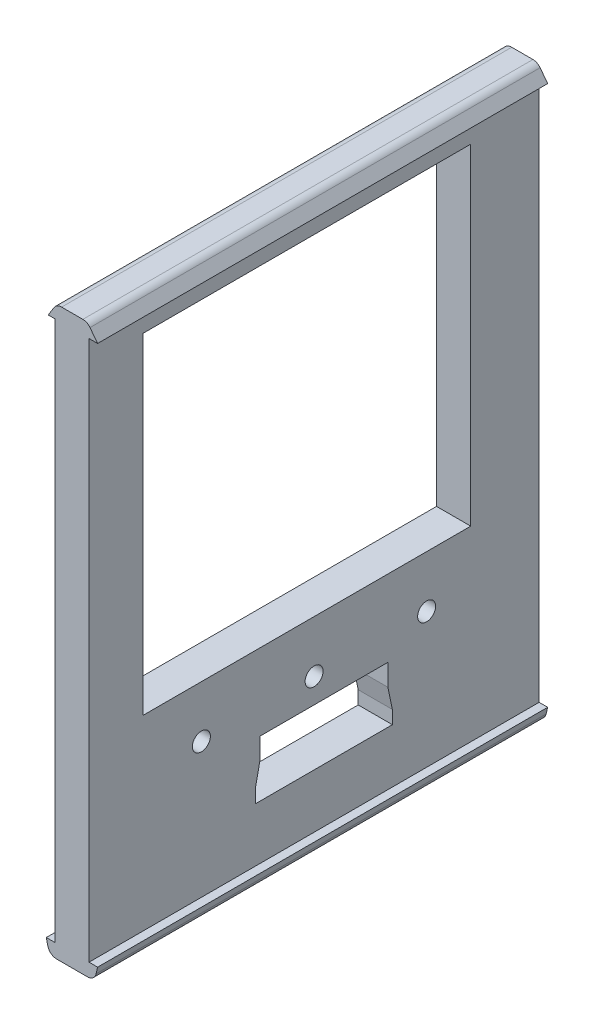
SolidWorks part; units mm, degrees
ref_plane "Plano frontal" through (0, 0, 0) normal (0, 0, 1) x (1, 0, 0)
ref_plane "Plano superior" through (0, 0, 0) normal (0, 1, 0) x (1, 0, 0)
ref_plane "Plano direito" through (0, 0, 0) normal (1, 0, 0) x (0, 0, -1)
sketch "Esboço1" plane through (0, 0, 0) normal (0, 0, 1) x (1, 0, 0)
  line L0 (0, 0) -> (0, 14.1176) construction
  line L1 (-3.8, -98.1786) -> (-5.7, -98.1786)
  line L2 (0, -101.1786) -> (0, -98.1786) construction
  line L3 (0, -98.1786) -> (-3.8, -98.1786) construction
  line L4 (-3.4129, -101.1786) -> (3.4129, -101.1786)
  line L5 (3.8, -98.1786) -> (0, -98.1786) construction
  line L6 (5.7, -98.1786) -> (5.7, -30.5351) construction
  line L7 (-5.3606, -99.6331) -> (-5.7, -98.1786)
  line L8 (5.7, -98.1786) -> (5.3606, -99.6331)
  line L9 (5.7, -30.5351) -> (5.7, 21.8214) construction
  line L10 (5.7, 21.8214) -> (3.4129, 21.8214) construction
  line L11 (3.8, -98.1786) -> (3.8, 21.8214)
  line L12 (3.8, 21.8214) -> (3.4129, 21.8214)
  line L13 (-3.8, -98.1786) -> (-3.8, 21.8214)
  line L14 (3.8, -98.1786) -> (5.7, -98.1786)
  line L15 (-5.2668, 21.8214) -> (-5.2668, 17.6583) construction
  line L16 (3.4129, -101.1786) -> (3.4129, 21.8214) construction
  line L17 (-3.4129, -101.1786) -> (-3.4129, 24.8214) construction
  line L18 (5.7, 21.8214) -> (3.4129, 21.8214)
  line L19 (3.4129, 21.8214) -> (3.4129, 24.8214) construction
  line L20 (5.7, 21.8214) -> (4.0133, 24.0339)
  line L21 (2.4227, 24.8214) -> (-2.2978, 24.8214)
  line L22 (-3.9992, 23.8727) -> (-5.2668, 21.8214)
  line L23 (-3.4129, 21.8214) -> (-5.2668, 21.8214) construction
  line L24 (-3.4129, 21.8214) -> (-3.8, 21.8214)
  line L25 (-3.4129, 21.8214) -> (-5.2668, 21.8214)
  arc A0 (3.4129, -101.1786) -> (5.3606, -99.6331) centre (3.4129, -99.1786) ccw
  arc A1 (-5.3606, -99.6331) -> (-3.4129, -101.1786) centre (-3.4129, -99.1786) ccw
  arc A2 (-2.2978, 24.8214) -> (-3.9992, 23.8727) centre (-2.2978, 22.8214) ccw
  arc A3 (2.4227, 24.8214) -> (4.0133, 24.0339) centre (2.4227, 22.8214) cw
  point P15 (5, -101.1786)
  point P18 (-5, -101.1786)
  dimension "D9" = 2
  dimension "D11" = 2
  dimension "D1" = 5.7
  dimension "D2" = 5.7
  dimension "D3" = 11.4
  dimension "D4" = 5.7
  dimension "D5" = 5
  dimension "D6" = 7.6
  dimension "D7" = 3.8
  dimension "D8" = 120
  dimension "D10" = 3
  dimension "D12" = 3
extrude "Ressalto-extrusão1" add sketch "Esboço1" along normal blind 160
sketch "Esboço2" plane through (0, 0, 0) normal (0, 0, 1) x (1, 0, 0)
  line L1 (-3.8, 21.8214) -> (3.8, 21.8214)
  line L2 (-3.8, 21.8214) -> (-3.8, -98.1786)
  line L3 (-3.8, -98.1786) -> (3.8, -98.1786)
  line L4 (3.8, 21.8214) -> (3.8, -98.1786)
extrude "Corte-extrusão1" cut sketch "Esboço2" along normal blind 30
sketch3d "3DSketch2"
  line L1 (-3.8, 21.8214, 160) -> (3.8, 21.8214, 160)
  line L2 (-3.8, 21.8214, 160) -> (-3.8, -98.1786, 160)
  line L3 (-3.8, -98.1786, 160) -> (3.8, -98.1786, 160)
  line L4 (3.8, 21.8214, 160) -> (3.8, -98.1786, 160)
  dimension "D1" = 160
extrude "Corte-extrusão2" cut sketch "3DSketch2" along direction (0, 0, 1) on the side of the normal blind 30
sketch3d "3DSketch3"
  line L0 (3.8, 21.8214, 130) -> (3.8, 21.8214, 80) construction
  line L1 (3.8, 21.8214, 130) -> (3.8, 21.8214, 30) construction
  line L2 (3.8, 21.8214, 80) -> (3.8, -98.1786, 80) construction
  line L3 (3.8, -98.1786, 130) -> (3.8, -98.1786, 30) construction
  line L4 (3.8, -98.1786, 80) -> (3.8, -98.1786, 130) construction
  line L5 (3.8, -98.1786, 130) -> (3.8, -38.1786, 130) construction
  line L6 (3.8, -98.1786, 130) -> (3.8, 21.8214, 130) construction
  line L7 (3.8, -38.1786, 130) -> (3.8, -38.1786, 30) construction
  line L8 (3.8, -98.1786, 30) -> (3.8, 21.8214, 30) construction
  line L9 (3.8, 21.8214, 130) -> (3.8, -98.1786, 30) construction
  line L10 (3.8, -98.1786, 30) -> (3.8, -98.1786, 130) construction
  line L11 (3.8, -98.1786, 130) -> (3.8, 21.8214, 30) construction
  line L12 (3.8, 21.8214, 30) -> (3.8, -38.1786, 130) construction
  line L13 (3.8, -38.1786, 130) -> (3.8, 21.8214, 130) construction
  line L14 (3.8, 21.8214, 130) -> (3.8, -38.1786, 30) construction
  line L15 (3.8, -38.1786, 30) -> (3.8, -8.1786, 30) construction
  line L16 (3.8, -8.1786, 30) -> (3.8, -8.1786, 130) construction
  line L17 (3.8, -38.1786, 130) -> (3.8, -98.1786, 30) construction
  line L18 (3.8, -98.1786, 30) -> (3.8, -98.1786, 130) construction
  line L19 (3.8, -98.1786, 130) -> (3.8, -38.1786, 30) construction
  line L20 (3.8, -68.1786, 80) -> (3.8, -68.1786, 30) construction
  line L21 (3.8, -68.1786, 30) -> (3.8, -68.1786, 130) construction
  line L22 (3.8, 21.8214, 105) -> (3.8, -98.1786, 80) construction
  line L23 (3.8, -98.1786, 80) -> (3.8, -98.1786, 105) construction
  line L24 (3.8, -98.1786, 105) -> (3.8, 21.8214, 80) construction
  line L25 (3.8, 21.8214, 80) -> (3.8, -98.1786, 55) construction
  line L26 (3.8, -98.1786, 55) -> (3.8, 21.8214, 55) construction
  line L27 (3.8, 21.8214, 55) -> (3.8, -98.1786, 80) construction
  line L28 (3.8, -98.1786, 80) -> (3.8, -38.1786, 67.5) construction
  line L29 (3.8, -38.1786, 67.5) -> (3.8, -98.1786, 67.5) construction
  line L30 (3.8, -98.1786, 67.5) -> (3.8, 21.8214, 67.5) construction
  line L31 (3.8, -38.1786, 92.5213) -> (3.8, 21.8214, 92.5213) construction
  line L32 (3.8, 21.8214, 92.5213) -> (3.8, -98.1786, 92.5213) construction
  circle A0 centre (3.8, -38.1786, 80) radius 2
  circle A1 centre (3.8, -8.1786, 80) radius 2
  circle A2 centre (3.8, -68.1786, 80) radius 2
  circle A3 centre (3.8, -68.1786, 55) radius 2
  circle A4 centre (3.8, -38.1786, 55) radius 2
  circle A5 centre (3.8, -8.1786, 55) radius 2
  circle A6 centre (3.8, -68.1786, 105.0426) radius 2
  circle A7 centre (3.8, -38.1786, 105.0426) radius 2
  circle A8 centre (3.8, -8.1786, 105.0426) radius 2
  point P18 (5.8, -38.1786, 80)
  point P27 (5.8, -8.1786, 80)
  point P32 (5.8, -68.1786, 80)
  point P42 (5.8, -68.1786, 55)
  point P45 (5.8, -38.1786, 55)
  point P48 (5.8, -8.1786, 55)
  point P54 (5.8, -68.1786, 105.0426)
  point P57 (5.8, -38.1786, 105.0426)
  point P60 (5.8, -8.1786, 105.0426)
extrude "Corte-extrusão3" cut sketch "3DSketch3" along direction (-1, 0, 0) on the side against the normal blind 70
sketch "Esboço3" plane through (0, 0, 0) normal (1, 0, 0) x (0, 0, -1)
  line L0 (-130, 21.8214) -> (-130, 24.8214) construction
  line L1 (-160, 24.8214) -> (0, 24.8214) construction
  line L2 (-130, 24.8214) -> (-30, 21.8214) construction
  line L3 (-30, 21.8214) -> (-30, 24.8214) construction
  line L4 (-30, -98.1786) -> (-30, -101.1786) construction
  line L5 (-160, -101.1786) -> (0, -101.1786) construction
  line L6 (-30, -101.1786) -> (-130, -98.1786) construction
  line L7 (-130, -98.1786) -> (-130, -101.1786) construction
  line L9 (-30, 24.8214) -> (15.0153, 24.8214)
  line L10 (-30, 24.8214) -> (-30, -104.6572)
  line L11 (-30, -104.6572) -> (15.0153, -104.6572)
  line L12 (15.0153, 24.8214) -> (15.0153, -104.6572)
  line L13 (-130, 24.8214) -> (-167.1926, 24.8214)
  line L14 (-130, 24.8214) -> (-130, -104.6572)
  line L15 (-130, -104.6572) -> (-167.1926, -104.6572)
  line L16 (-167.1926, 24.8214) -> (-167.1926, -104.6572)
  circle A0 centre (-80, -8.1786) radius 2 construction
extrude "Corte-extrusão4" cut sketch "Esboço3" along normal blind 41 and the other way blind 22
sketch "Esboço4" plane through (0, 0, 0) normal (1, 0, 0) x (0, 0, -1)
  line L1 (-118, 16.8214) -> (-45.2, 16.8214)
  line L2 (-118, 16.8214) -> (-118, -56.6786)
  line L3 (-118, -56.6786) -> (-45.2, -56.6786)
  line L4 (-45.2, 16.8214) -> (-45.2, -56.6786)
  line L5 (-93.0575, -86.1786) -> (-62.6075, -86.1786)
  line L6 (-92.0575, -78.466) -> (-92.0575, -73.6786)
  line L7 (-92.0575, -73.6786) -> (-63.6075, -73.6786)
  line L8 (-63.6075, -78.466) -> (-63.6075, -73.6786)
  line L9 (-93.0575, -83.2534) -> (-92.0575, -78.466)
  line L10 (-93.0575, -86.1786) -> (-93.0575, -83.2534)
  line L12 (-62.6075, -86.1786) -> (-62.6075, -83.2534)
  line L13 (-62.6075, -83.2534) -> (-63.6075, -78.466)
  dimension "D1" = 8
  dimension "D2" = 72.8
  dimension "D3" = 12
  dimension "D4" = 73.5
  dimension "D8" = 30.45
extrude "Corte-extrusão5" cut sketch "Esboço4" along direction (-1, 0, 0) on the side against the normal blind 36 and the other way blind 34
